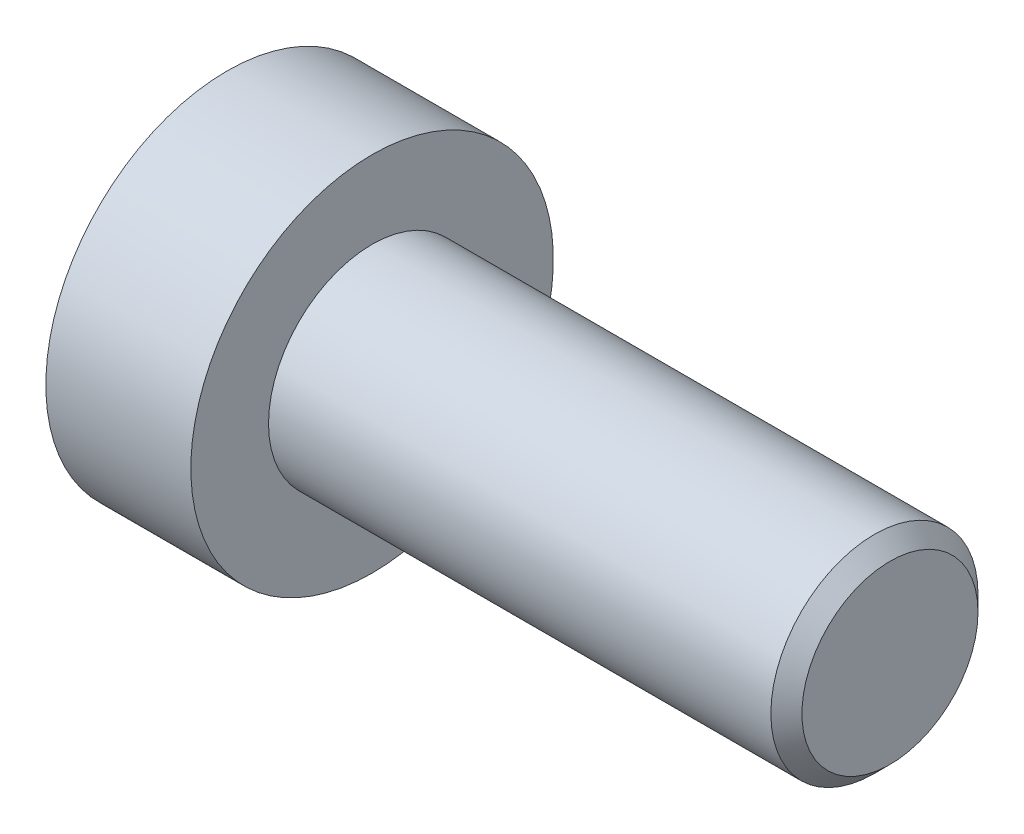
SolidWorks part; units mm, degrees
material "Plain Carbon Steel"
ref_plane "Front Plane" through (0, 0, 0) normal (0, 0, 1) x (1, 0, 0)
ref_plane "Top Plane" through (0, 0, 0) normal (0, 1, 0) x (1, 0, 0)
ref_plane "Right Plane" through (0, 0, 0) normal (1, 0, 0) x (0, 0, -1)
sketch "Sketch2" plane through (0, 0, 0) normal (1, 0, 0) x (0, 0, -1)
  circle A0 centre (0, 0) radius 2
  dimension "D1" = 4
extrude "Boss-Extrude1" add sketch "Sketch2" against normal blind 10
chamfer "Chamfer1" distance 0.3 angle 45 1 edges at (0, 0, -2)
sketch "Sketch6" plane through (0, 0, 0) normal (0, 0, 1) x (1, 0, 0)
  line L0 (-12.8, 0) -> (-12.8, 3.5)
  line L1 (-12.8, 0) -> (-10, 0)
  line L2 (-12.8, 3.5) -> (-10, 3.5)
  line L6 (-10, 3.5) -> (-10, 0)
  line L8 (-10, 0) -> (-14.6471, 0) construction
  line L10 (-10, 2) -> (-10, -2) construction
  dimension "D1" = 2.8
  dimension "D2" = 7
revolve "Revolve1" add sketch "Sketch6" angle 360 about L8
sketch "Sketch7" plane through (-12.8, 0, 0) normal (-1, 0, 0) x (0, 0, 1)
  line L1 (0, 1.4434) -> (-1.25, 0.7217)
  line L2 (-1.25, 0.7217) -> (-1.25, -0.7217)
  line L3 (-1.25, -0.7217) -> (0, -1.4434)
  line L4 (0, -1.4434) -> (1.25, -0.7217)
  line L5 (1.25, -0.7217) -> (1.25, 0.7217)
  line L6 (1.25, 0.7217) -> (0, 1.4434)
  circle A0 centre (0, 0) radius 1.25 construction
  dimension "D1" = 2.5
extrude "Cut-Extrude1" cut sketch "Sketch7" against normal blind 1.6
sketch "Sketch8" plane through (-12.8, 0, 0) normal (-1, 0, 0) x (0, 0, 1)
  circle A0 centre (0, 0) radius 1.4934
  dimension "D1" = 0.05
extrude "Cut-Extrude2" cut sketch "Sketch8" against normal blind 1 draft 45
